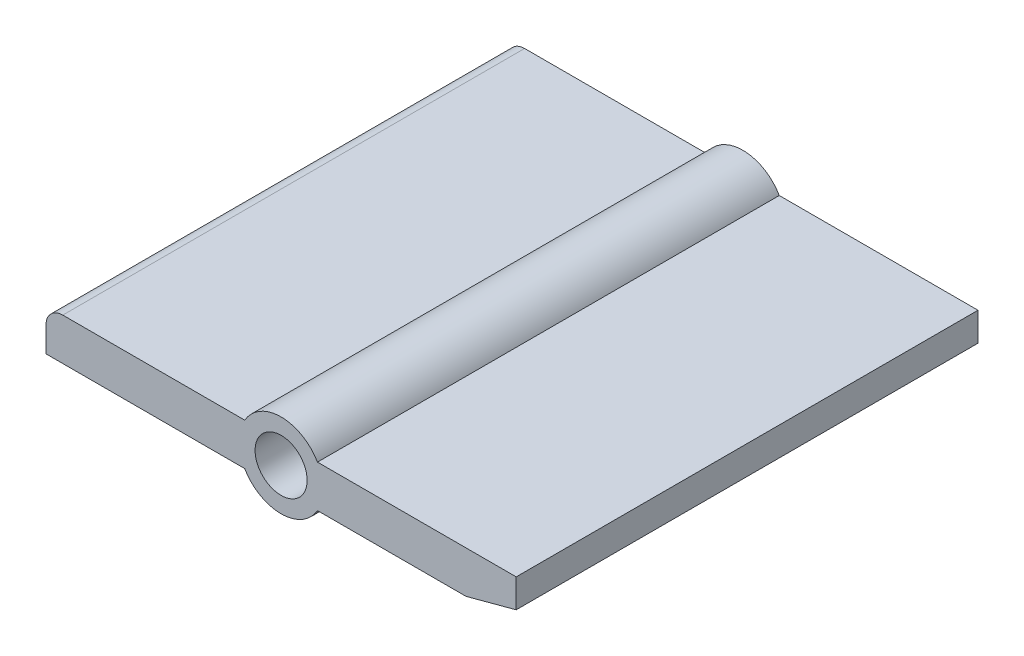
SolidWorks part; units mm, degrees
ref_plane "前视基准面" through (0, 0, 0) normal (0, 0, 1) x (1, 0, 0)
ref_plane "上视基准面" through (0, 0, 0) normal (0, 1, 0) x (1, 0, 0)
ref_plane "右视基准面" through (0, 0, 0) normal (1, 0, 0) x (0, 0, -1)
sketch "草图1" plane through (0, 0, 0) normal (0, 0, 1) x (1, 0, 0)
  line L0 (2.1651, 1.25) -> (14, 1.25)
  line L1 (-13, 1.25) -> (-2.1651, 1.25)
  line L2 (-14, 0.25) -> (-14, -1.25)
  line L3 (-14, -1.25) -> (-2.1651, -1.25)
  line L4 (14, 1.25) -> (14, -0.45)
  line L5 (-1.5439, 0.1378) -> (1.5439, -0.1378) construction
  line L6 (-1.5439, -0.1378) -> (1.5439, 0.1378) construction
  line L7 (2.1651, -1.25) -> (11.0144, -1.25)
  line L8 (14, -0.45) -> (11.0144, -1.25)
  arc A0 (-2.1651, -1.25) -> (2.1651, -1.25) centre (0, 0) ccw
  arc A1 (2.1651, 1.25) -> (-2.1651, 1.25) centre (0, 0) ccw
  circle A2 centre (0, 0) radius 1.55
  arc A3 (-14, 0.25) -> (-13, 1.25) centre (-13, 0.25) cw
  point P3 (14, -1.25)
  point P17 (-14, 1.25)
  dimension "D3" = 5
  dimension "D4" = 3.1
  dimension "D5" = 1
  dimension "D1" = 2.5
  dimension "D2" = 28
  dimension "D6" = 0.8
  dimension "D7" = 75
extrude "凸台-拉伸1" add sketch "草图1" along normal blind 27.5
